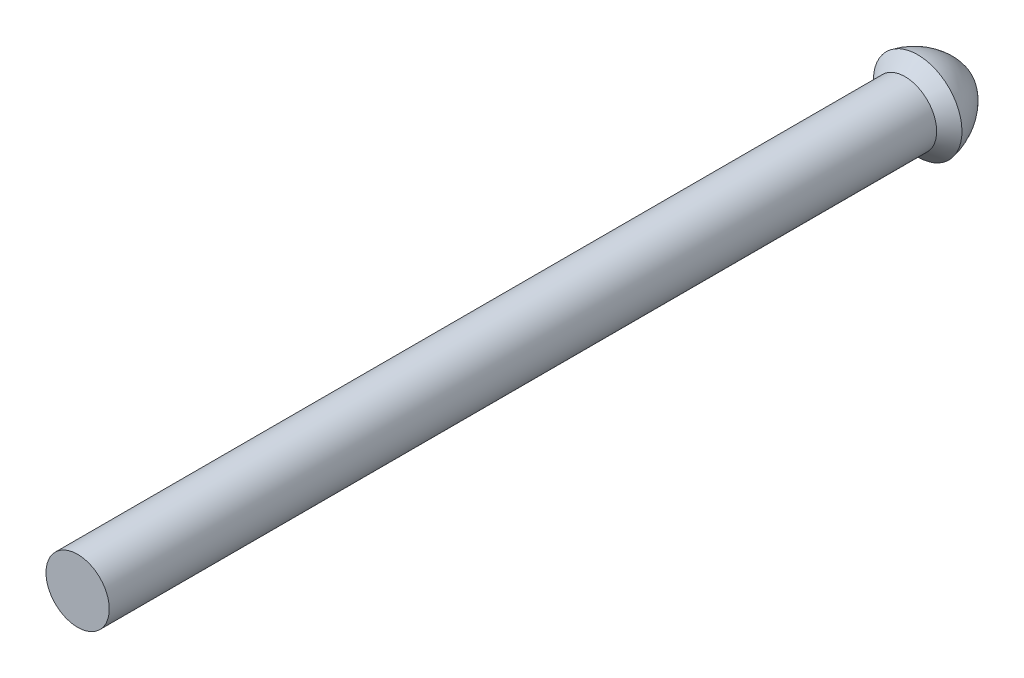
SolidWorks part; units mm, degrees
ref_plane "Front Plane" through (0, 0, 0) normal (0, 0, 1) x (1, 0, 0)
ref_plane "Top Plane" through (0, 0, 0) normal (0, 1, 0) x (1, 0, 0)
ref_plane "Right Plane" through (0, 0, 0) normal (1, 0, 0) x (0, 0, -1)
sketch "Sketch1" plane through (0, 0, 0) normal (1, 0, 0) x (0, 0, -1)
  line L0 (99.6299, 3.81) -> (101.1539, 5.334)
  line L1 (0, 0) -> (107.2371, 0)
  line L2 (0, 0) -> (0, 3.81)
  line L3 (0, 3.81) -> (99.6299, 3.81)
  line L5 (101.1539, 5.334) -> (101.1539, 0) construction
  line L7 (99.6299, 3.81) -> (99.6299, -2.54) construction
  arc A1 (107.2371, 0) -> (101.1539, 5.334) centre (99.6299, -2.54) ccw
  dimension "D1" = 99.6299
  dimension "D2" = 3.81
  dimension "D3" = 135
  dimension "D4" = 5.334
  dimension "D5" = 6.35
revolve "Revolve2" add sketch "Sketch1" angle 360 about L1
